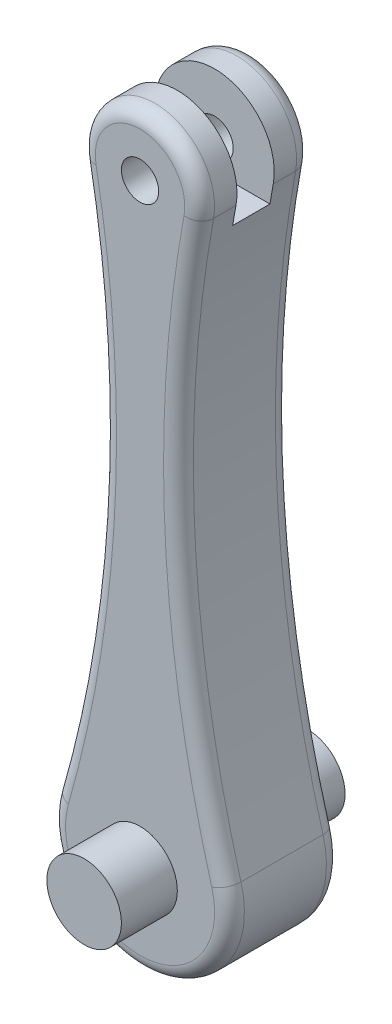
SolidWorks part; units mm, degrees
material "Cobre"
ref_plane "Front Plane" through (0, 0, 0) normal (0, 0, 1) x (1, 0, 0)
ref_plane "Top Plane" through (0, 0, 0) normal (0, 1, 0) x (1, 0, 0)
ref_plane "Right Plane" through (0, 0, 0) normal (1, 0, 0) x (0, 0, -1)
sketch "Sketch1" plane through (0, 0, 0) normal (0, 0, 1) x (1, 0, 0)
  line L1 (0, 7) -> (0, 59.6229) construction
  circle A4 centre (0, 80) radius 2.5
  arc A5 (7.8684, 78.5549) -> (-7.8684, 78.5549) centre (0, 80) ccw
  arc A6 (-11.5359, 3.3051) -> (11.5359, 3.3051) centre (0, 0) ccw
  arc A8 (7.8684, 78.5549) -> (11.5359, 3.3051) centre (170.1542, 48.75) ccw
  arc A9 (-11.5359, 3.3051) -> (-7.8684, 78.5549) centre (-170.1542, 48.75) ccw
  dimension "D1" = 24
  dimension "D3" = 16
  dimension "D4" = 330
  dimension "D2" = 5
  dimension "D5" = 330
extrude "Boss-Extrude1" add sketch "Sketch1" along normal blind 15
fillet "Fillet4" radius 2 8 edges at (0, -12, 15) (-5.3498, 40.7179, 15) (0, -12, 0) (-5.3498, 40.7179, 0) (5.3498, 40.7179, 15) (5.3498, 40.7179, 0) (0, 88, 15) (0, 88, 0)
sketch "Sketch9" plane through (0, 0, 0) normal (1, 0, 0) x (0, 0, -1)
  line L1 (-15, 82.5) -> (-15, 77.5) construction
  line L9 (-5, 76) -> (-10, 76)
  line L10 (-5, 76) -> (-5, 88)
  line L11 (-5, 88) -> (-10, 88)
  line L12 (-10, 76) -> (-10, 88)
  line L13 (-5, 76) -> (-10, 88) construction
  line L14 (-5, 88) -> (-10, 76) construction
  point P2 (-7.5, 82)
  dimension "D1" = 5
  dimension "D2" = 5
  dimension "D3" = 12
extrude "Cut-Extrude1" cut sketch "Sketch9" against normal through all and the other way through all
sketch "Sketch10" plane through (0, 0, 0) normal (0, 0, 1) x (1, 0, 0)
  circle A0 centre (0, 0) radius 5
  dimension "D1" = 10
extrude "Boss-Extrude2" add sketch "Sketch10" along normal blind 22.5 and the other way blind 7.5
